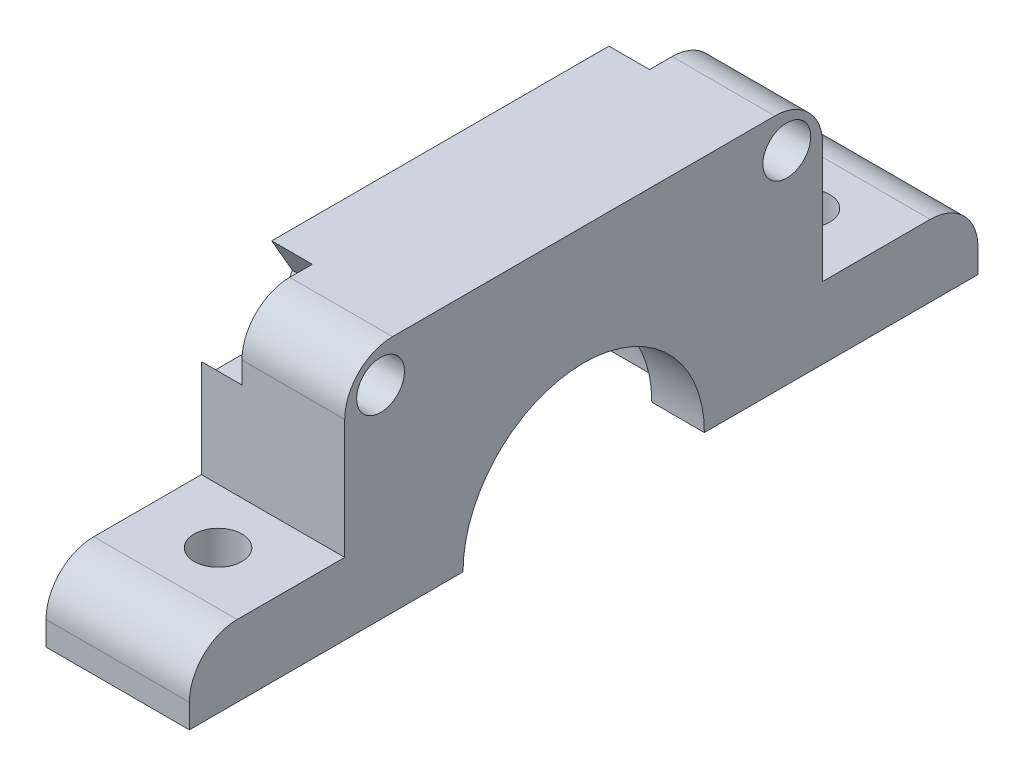
SolidWorks part; units mm, degrees
ref_plane "Front Plane" through (0, 0, 0) normal (0, 0, 1) x (1, 0, 0)
ref_plane "Top Plane" through (0, 0, 0) normal (0, 1, 0) x (1, 0, 0)
ref_plane "Right Plane" through (0, 0, 0) normal (1, 0, 0) x (0, 0, -1)
sketch "Sketch1" plane through (0, 0, 0) normal (0, 1, 0) x (1, 0, 0)
  line L1 (3.9216, 23.2941) -> (9.9216, 23.2941)
  line L2 (3.9216, 23.2941) -> (3.9216, -9.7059)
  line L3 (3.9216, -9.7059) -> (9.9216, -9.7059)
  line L4 (9.9216, 23.2941) -> (9.9216, -9.7059)
  dimension "D1" = 33
  dimension "D2" = 6
extrude "Boss-Extrude1" add sketch "Sketch1" along normal blind 3
sketch "Sketch3" plane through (9.9216, 0, 0) normal (1, 0, 0) x (0, 0, -1)
  line L0 (16.7941, 0) -> (16.7941, 10)
  line L1 (-9.7059, 0) -> (23.2941, 0) construction
  line L2 (16.7941, 0) -> (-3.2059, 0)
  line L3 (-3.2059, 0) -> (-3.2059, 10)
  line L4 (-3.2059, 10) -> (16.7941, 10)
  point P7 (6.7941, 0)
  point P9 (6.7941, 0)
  dimension "D1" = 20
  dimension "D2" = 10
extrude "Boss-Extrude2" add sketch "Sketch3" against normal blind 6
fillet "Fillet1" radius 2 2 edges at (6.9216, 10, -16.7941) (6.9216, 10, 3.2059)
sketch "Sketch4" plane through (3.9216, 0, 0) normal (-1, 0, 0) x (0, 0, 1)
  line L0 (-23.2941, 0) -> (9.7059, 0) construction
  line L1 (-11.8441, 0) -> (-1.7441, 0)
  arc A0 (-11.8441, 0) -> (-1.7441, 0) centre (-6.7941, 0) cw
  dimension "D1" = 5.05
extrude "Cut-Extrude1" cut sketch "Sketch4" against normal blind 43
sketch "Sketch5" plane through (3.9216, 0, 0) normal (-1, 0, 0) x (0, 0, 1)
  circle A0 centre (-6.7941, 0) radius 6.05
  dimension "D1" = 12.1
extrude "Cut-Extrude2" cut sketch "Sketch5" against normal blind 3.8
fillet "Fillet2" radius 2 2 edges at (6.9216, 3, -23.2941) (6.9216, 3, 9.7059)
sketch "Sketch6" plane through (0, 3, 0) normal (0, 1, 0) x (1, 0, 0)
  line L0 (6.9216, 19.0941) -> (6.9216, -5.5059) construction
  line L1 (3.9216, -7.7059) -> (9.9216, -7.7059) construction
  line L2 (3.9216, -9.7059) -> (9.9216, -9.7059) construction
  line L3 (9.9216, -9.7059) -> (3.9216, -9.7059) construction
  circle A0 centre (6.9216, -5.5059) radius 1
  circle A1 centre (6.9216, 19.0941) radius 1
  point P4 (6.9216, 6.7941)
  point P7 (6.9216, -7.7059)
  dimension "D3" = 2
  dimension "D1" = 16.5
  dimension "D2" = 4.2
extrude "Cut-Extrude3" cut sketch "Sketch6" against normal blind 3.8
sketch "Sketch7" plane through (9.9216, 0, 0) normal (1, 0, 0) x (0, 0, -1)
  line L0 (-1.7059, 8.5) -> (15.2941, 8.5) construction
  line L1 (14.7941, 10) -> (-1.2059, 10) construction
  line L2 (-9.7059, 0) -> (1.7441, 0) construction
  circle A0 centre (-1.7059, 8.5) radius 1
  circle A1 centre (15.2941, 8.5) radius 1
  point P9 (6.7941, 10)
  point P10 (6.7941, 8.5)
  dimension "D1" = 2
  dimension "D2" = 17
  dimension "D3" = 8.5
extrude "Cut-Extrude4" cut sketch "Sketch7" against normal blind 15
sketch "Sketch8" plane through (3.9216, 0, 0) normal (-1, 0, 0) x (0, 0, 1)
  line L1 (-0.6035, 8.5) -> (0.5512, 6.5)
  line L2 (0.5512, 6.5) -> (2.8606, 6.5)
  line L3 (2.8606, 6.5) -> (4.0153, 8.5)
  line L4 (4.0153, 8.5) -> (2.8606, 10.5)
  line L5 (2.8606, 10.5) -> (0.5512, 10.5)
  line L6 (0.5512, 10.5) -> (-0.6035, 8.5)
  line L7 (-17.6035, 8.5) -> (-16.4488, 6.5)
  line L8 (-16.4488, 6.5) -> (-14.1394, 6.5)
  line L9 (-14.1394, 6.5) -> (-12.9847, 8.5)
  line L10 (-12.9847, 8.5) -> (-14.1394, 10.5)
  line L11 (-14.1394, 10.5) -> (-16.4488, 10.5)
  line L12 (-16.4488, 10.5) -> (-17.6035, 8.5)
  circle A0 centre (1.7059, 8.5) radius 2 construction
  circle A1 centre (-15.2941, 8.5) radius 2 construction
  dimension "D1" = 4
extrude "Cut-Extrude5" cut sketch "Sketch8" against normal blind 1.7
